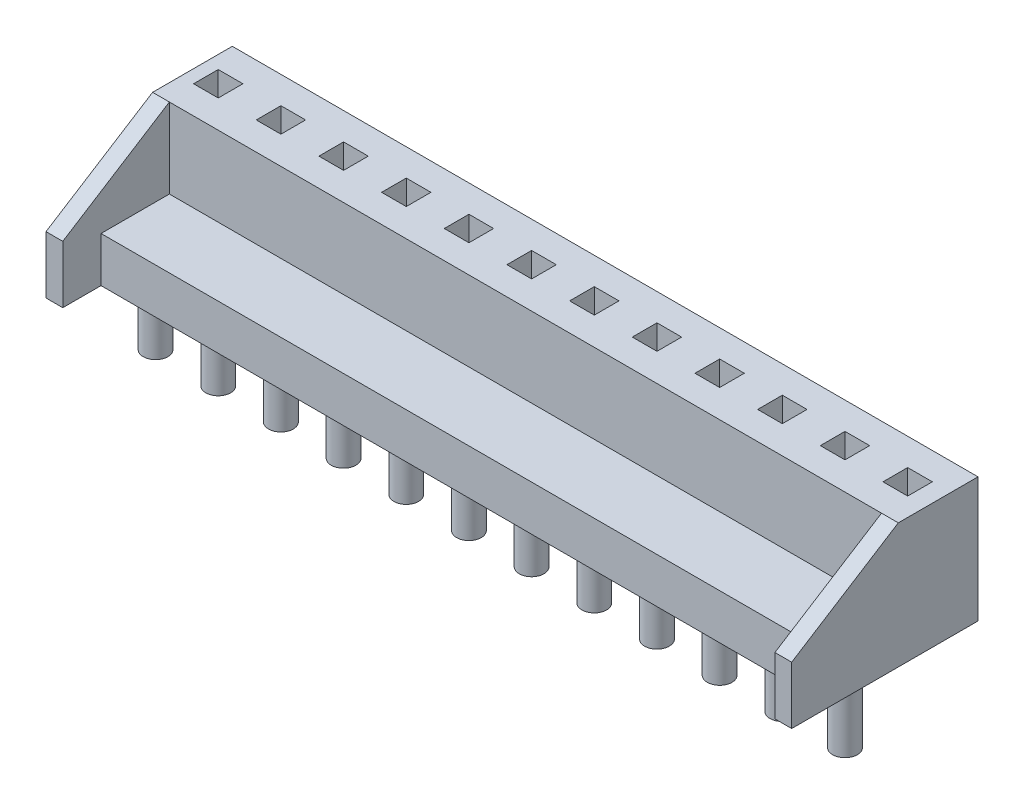
SolidWorks part; units mm, degrees
ref_plane "Front Plane" through (0, 0, 0) normal (0, 0, 1) x (1, 0, 0)
ref_plane "Top Plane" through (0, 0, 0) normal (0, 1, 0) x (1, 0, 0)
ref_plane "Right Plane" through (0, 0, 0) normal (1, 0, 0) x (0, 0, -1)
sketch "Sketch1" plane through (0, 0, 0) normal (1, 0, 0) x (0, 0, -1)
  line L0 (-2.77, 0) -> (3.23, 0)
  line L1 (3.23, 0) -> (3.23, 5.06)
  line L2 (3.23, 5.06) -> (0, 5.06)
  line L3 (0, 5.06) -> (0, 1.83)
  line L4 (0, 1.83) -> (-2.77, 1.83)
  line L5 (-2.77, 1.83) -> (-2.77, 0)
  dimension "D1" = 6
  dimension "D2" = 3.23
  dimension "D3" = 5.06
  dimension "D4" = 1.83
extrude "Boss-Extrude1" add sketch "Sketch1" along normal mid plane 30.22 contours L4 L5 L0 L1 L2 L3
sketch "Sketch2" plane through (15.11, 0, 0) normal (1, 0, 0) x (0, 0, -1)
  line L0 (-4.32, 0) -> (-4.32, 2.33)
  line L1 (-4.32, 2.33) -> (0, 5.06)
  line L2 (0, 5.06) -> (0, 0)
  line L3 (0, 0) -> (-4.32, 0)
  line L4 (3.23, 0) -> (3.23, 5.06) construction
  dimension "D1" = 7.55
  dimension "D2" = 2.33
extrude "Boss-Extrude2" add sketch "Sketch2" against normal blind 0.68
mirror "Mirror1" about plane through (0, 0, 0) normal (1, 0, 0) of "Boss-Extrude2"
sketch "Sketch3" plane through (0, 5.06, 0) normal (0, 1, 0) x (1, 0, 0)
  line L0 (15.11, 3.23) -> (15.11, 0) construction
  line L1 (14.36, 1.13) -> (13.36, 1.13)
  line L2 (14.36, 1.13) -> (14.36, 2.13)
  line L3 (14.36, 2.13) -> (13.36, 2.13)
  line L4 (13.36, 1.13) -> (13.36, 2.13)
  line L5 (15.11, 3.23) -> (-15.11, 3.23) construction
  dimension "D1" = 1
  dimension "D2" = 1
  dimension "D3" = 0.75
  dimension "D4" = 1.1
extrude "Cut-Extrude1" cut sketch "Sketch3" against normal through all
sketch "Sketch4" plane through (0, 0, 0) normal (0, 1, 0) x (1, 0, 0)
  line L0 (13.36, 1.13) -> (14.36, 1.13) construction
  line L1 (14.36, 1.13) -> (14.36, 2.13) construction
  circle A0 centre (13.86, -0.91) radius 0.5
  point P4 (13.86, 1.13)
  point P5 (13.61, -0.4229)
  point P6 (13.61, -1.2888)
  point P9 (14.36, 1.63)
  dimension "D2" = 1
  dimension "D1" = 2.54
extrude "Boss-Extrude3" add sketch "Sketch4" against normal blind 3
pattern_linear "LPattern1" count 12 spacing 2.54 along (-1, 0, 0) of "Cut-Extrude1", "Boss-Extrude3"
